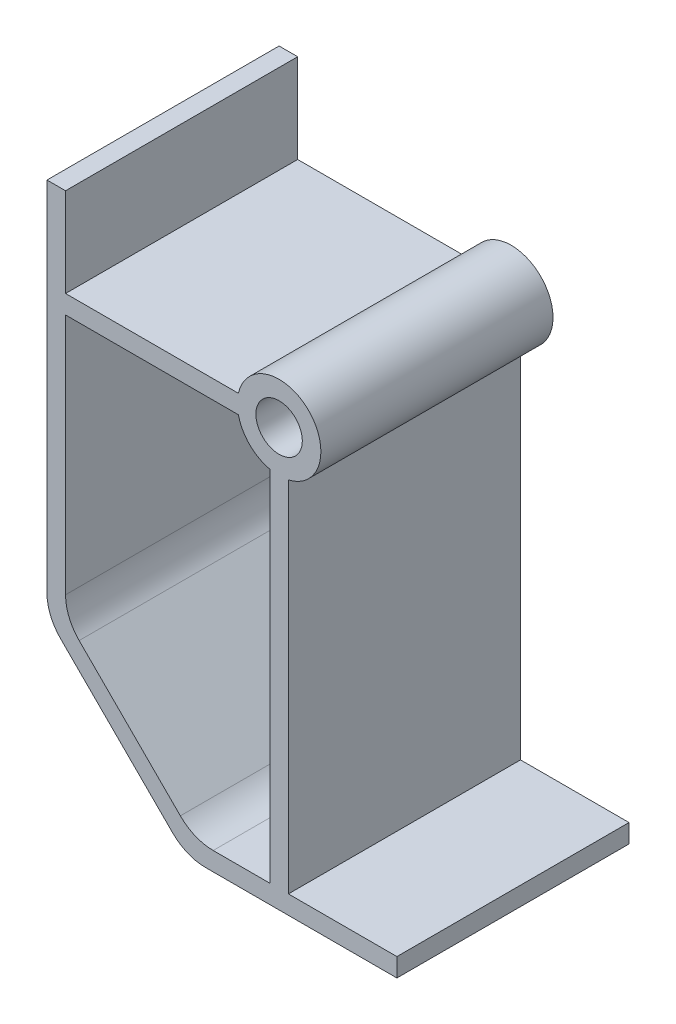
SolidWorks part; units mm, degrees
ref_plane "Front Plane" through (0, 0, 0) normal (0, 0, 1) x (1, 0, 0)
ref_plane "Top Plane" through (0, 0, 0) normal (0, 1, 0) x (1, 0, 0)
ref_plane "Right Plane" through (0, 0, 0) normal (1, 0, 0) x (0, 0, -1)
sketch "Sketch1" plane through (0, 0, 0) normal (0, 0, 1) x (1, 0, 0)
  line L0 (-25, 10.584) -> (-25, -30)
  line L1 (0, 10.584) -> (0, -45) construction
  line L2 (-25, 0) -> (12.687, 0) construction
  line L3 (-10, -45) -> (12.687, -45)
  line L4 (-12.2749, 0) -> (12.687, 0) construction
  line L5 (-23, 10.584) -> (-23, 1)
  line L6 (-23, -29.1716) -> (-9.1716, -43)
  line L7 (-25, -30) -> (-10, -45)
  line L8 (-9.1716, -43) -> (-1, -43)
  line L9 (-25, 10.584) -> (-25, -45) construction
  line L10 (-12.2749, -45) -> (12.687, -45) construction
  line L11 (-23, -1) -> (-4.3875, -1)
  line L13 (-23, 1) -> (-4.3875, 1)
  line L15 (-25, 10.584) -> (-23, 10.584)
  line L16 (-23, -1) -> (-23, -29.1716)
  line L17 (12.687, -43) -> (12.687, -45)
  line L18 (-25, 1) -> (12.687, 1) construction
  line L19 (-25, -1) -> (12.687, -1) construction
  line L20 (1, -43) -> (12.687, -43)
  line L21 (-23, 10.584) -> (-23, -29.1716) construction
  line L24 (-9.1716, -43) -> (12.687, -43) construction
  line L27 (-1, -4.3875) -> (-1, -43)
  line L28 (1, -4.3875) -> (1, -43)
  circle A0 centre (0, 0) radius 2.5
  arc A1 (1, -4.3875) -> (-4.3875, 1) centre (0, 0) ccw
  arc A2 (-4.3875, -1) -> (-1, -4.3875) centre (0, 0) ccw
  circle A3 centre (0, 0) radius 4.5 construction
  point P19 (12.687, -30)
  point P23 (-1, 10.584)
  point P24 (-1, -45)
  point P27 (1, 10.584)
  point P28 (1, -45)
  point P41 (4.5, 0)
  dimension "D1" = 5
  dimension "D5" = 10
  dimension "D6" = 30
  dimension "D8" = 1
  dimension "D3" = 25
  dimension "D7" = 2
  dimension "D9" = 1
  dimension "D11" = 1
  dimension "D10" = 1
  dimension "D2" = 2
  dimension "D4" = 45
extrude "Boss-Extrude1" add sketch "Sketch1" along normal blind 25
fillet "Fillet1" radius 5 4 edges at (-9.1716, -43, 12.5) (-25, -30, 12.5) (-23, -29.1716, 12.5) (-10, -45, 12.5)
